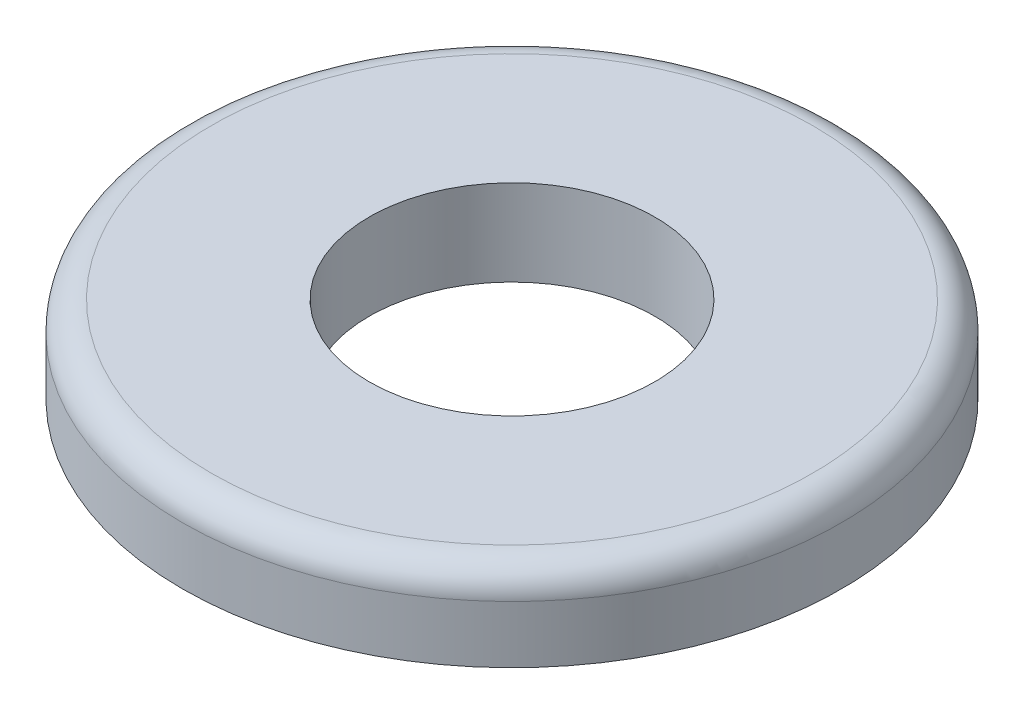
SolidWorks part; units mm, degrees
ref_plane "Front Plane" through (0, 0, 0) normal (0, 0, 1) x (1, 0, 0)
ref_plane "Top Plane" through (0, 0, 0) normal (0, 1, 0) x (1, 0, 0)
ref_plane "Right Plane" through (0, 0, 0) normal (1, 0, 0) x (0, 0, -1)
sketch "Sketch1" plane through (0, 0, 0) normal (0, 1, 0) x (1, 0, 0)
  circle A0 centre (0, 0) radius 18.2562
  circle A1 centre (0, 0) radius 7.9121
  dimension "D1" = 36.5125
  dimension "D2" = 15.8242
extrude "Boss-Extrude1" add sketch "Sketch1" along normal blind 4.7625
fillet "Fillet1" radius 1.5875 1 edges at (0, 4.7625, 18.2562)
